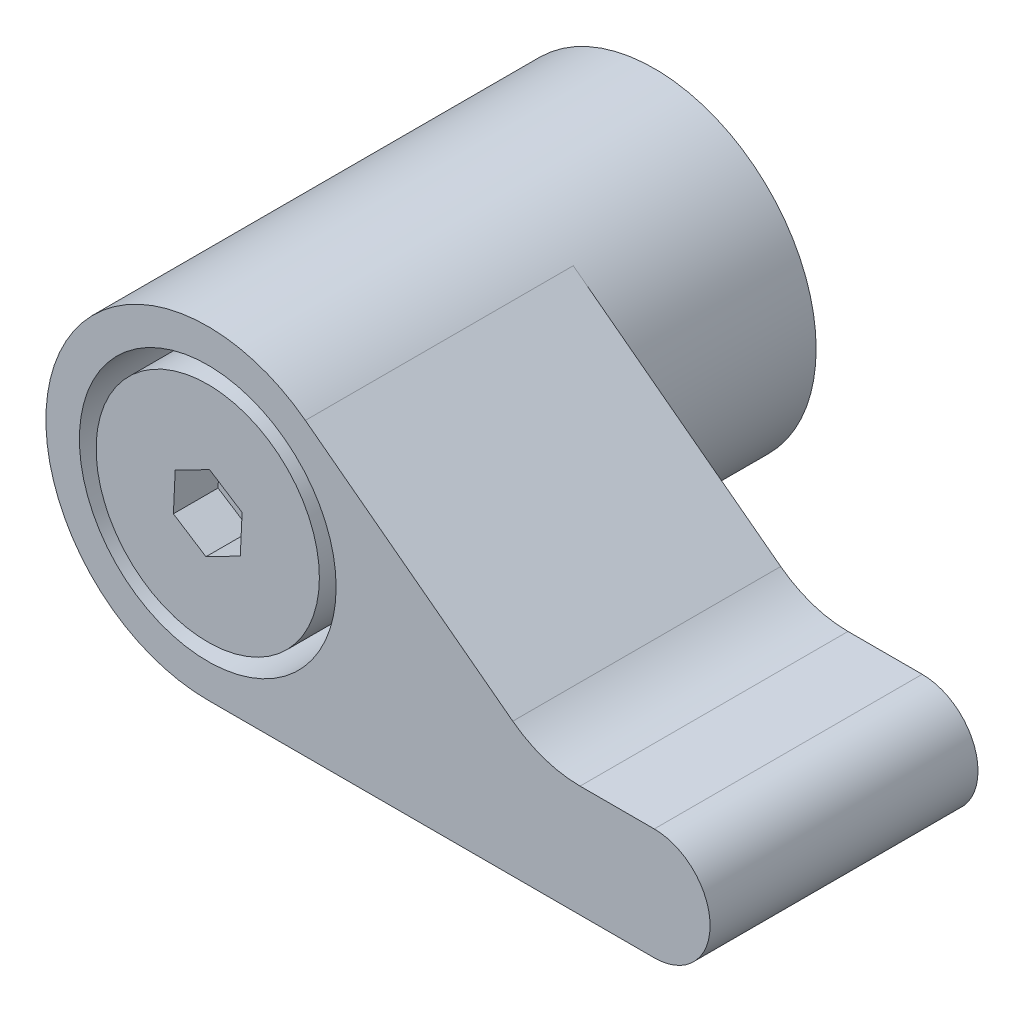
SolidWorks part; units mm, degrees
ref_plane "Спереди" through (0, 0, 0) normal (0, 0, 1) x (1, 0, 0)
ref_plane "Сверху" through (0, 0, 0) normal (0, 1, 0) x (1, 0, 0)
ref_plane "Справа" through (0, 0, 0) normal (1, 0, 0) x (0, 0, -1)
sketch "Эскиз1" plane through (0, 0, 0) normal (0, 0, 1) x (1, 0, 0)
  circle A0 centre (0, 0) radius 7.25
  dimension "D1" = 14.5
extrude "Бобышка-Вытянуть1" add sketch "Эскиз1" along normal blind 20
sketch "Эскиз2" plane through (0, 0, 20) normal (0, 0, 1) x (1, 0, 0)
  line L0 (0, -7.25) -> (20, -7.25)
  line L1 (20, -2.25) -> (15, -2.25)
  line L2 (15, -2.25) -> (4.3717, 5.7837)
  arc A0 (4.3717, 5.7837) -> (0, -7.25) centre (0, 0) ccw
  arc A1 (20, -7.25) -> (20, -2.25) centre (20, -4.75) ccw
  dimension "D1" = 14.5
  dimension "D2" = 20
  dimension "D3" = 5
  dimension "D4" = 5
extrude "Бобышка-Вытянуть2" add sketch "Эскиз2" against normal blind 12
fillet "Скругление1" radius 5 1 edges at (15, -2.25, 14)
sketch "Эскиз3" plane through (0, 0, 20) normal (0, 0, 1) x (1, 0, 0)
  circle A0 centre (0, 0) radius 5.75
  dimension "D1" = 11.5
extrude "Вырез-Вытянуть1" cut sketch "Эскиз3" against normal blind 10
sketch "Эскиз4" plane through (0, 0, 10) normal (0, 0, 1) x (1, 0, 0)
  circle A0 centre (0, 0) radius 5
  dimension "D1" = 10
extrude "Бобышка-Вытянуть3" add sketch "Эскиз4" along normal up to surface (10 mm away) up to face at (5.75, 0, 20)
sketch "Эскиз5" plane through (0, 0, 20) normal (0, 0, 1) x (1, 0, 0)
  line L1 (1.458, -0.935) -> (1.5388, 0.7951)
  line L2 (1.5388, 0.7951) -> (0.0808, 1.7302)
  line L3 (0.0808, 1.7302) -> (-1.458, 0.935)
  line L4 (-1.458, 0.935) -> (-1.5388, -0.7951)
  line L5 (-1.5388, -0.7951) -> (-0.0808, -1.7302)
  line L6 (-0.0808, -1.7302) -> (1.458, -0.935)
  circle A0 centre (0, 0) radius 1.5 construction
  dimension "D1" = 3
extrude "Вырез-Вытянуть2" cut sketch "Эскиз5" against normal blind 2
